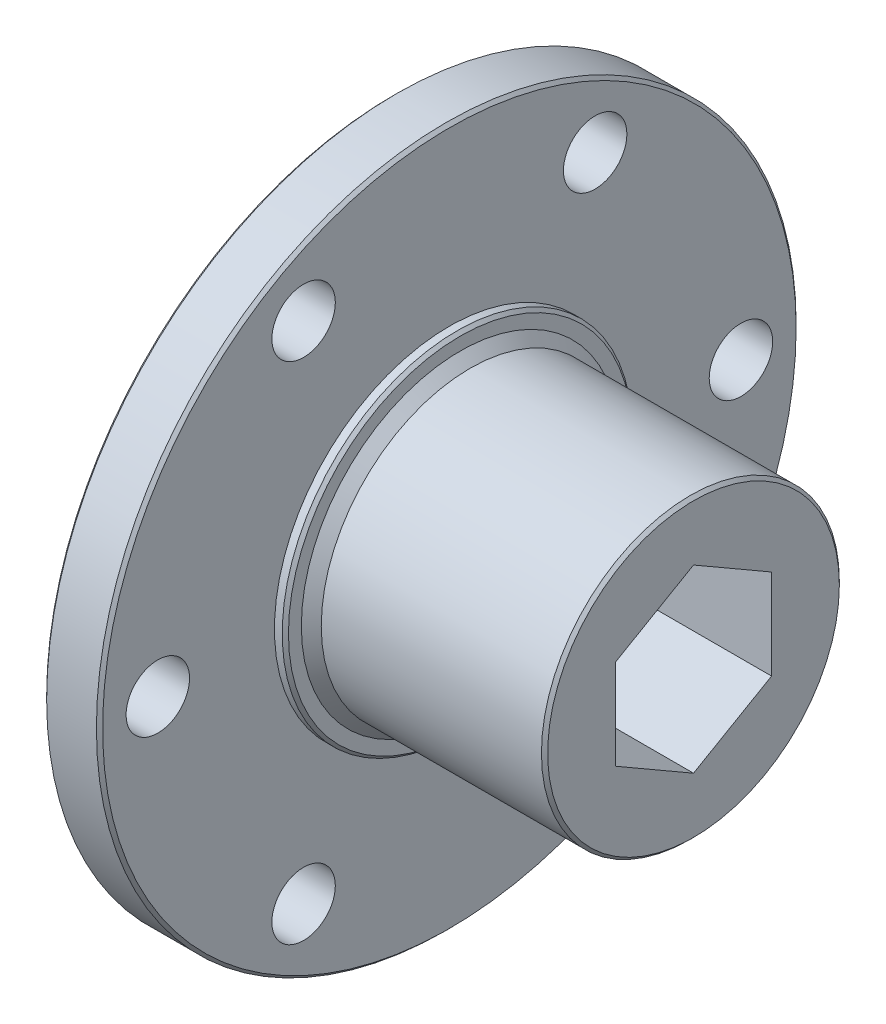
SolidWorks part; units mm, degrees
ref_plane "Front Plane" through (0, 0, 0) normal (0, 0, 1) x (1, 0, 0)
ref_plane "Top Plane" through (0, 0, 0) normal (0, 1, 0) x (1, 0, 0)
ref_plane "Right Plane" through (0, 0, 0) normal (1, 0, 0) x (0, 0, -1)
ref_plane "Plane4" through (0, 0, 0) normal (0, 0, -1) x (-1, 0, 0)
sketch "Sketch1" plane through (0, 0, 0) normal (0, 0, -1) x (-1, 0, 0)
  line L0 (13.9241, 28.575) -> (13.9241, 0)
  line L1 (13.9241, 0) -> (18.4961, 0)
  line L2 (18.4961, 0) -> (18.4961, 28.575)
  line L3 (18.4961, 28.575) -> (13.9241, 28.575)
  line L4 (13.9241, 0) -> (18.4961, 0) construction
revolve "Revolve1" add sketch "Sketch1" angle 360 about L4
sketch "Sketch2" plane through (-13.9241, 0, 0) normal (1, 0, 0) x (0, 0, -1)
  circle A0 centre (0, 0) radius 14.2875
extrude "Boss-Extrude1" add sketch "Sketch2" along normal blind 0.889
sketch "Sketch3" plane through (-13.0351, 0, 0) normal (1, 0, 0) x (0, 0, -1)
  circle A0 centre (0, 0) radius 12.9794
extrude "Boss-Extrude2" add sketch "Sketch3" along normal blind 0.8128 draft 45
sketch "Sketch4" plane through (-12.2223, 0, 0) normal (1, 0, 0) x (0, 0, -1)
  circle A0 centre (0, 0) radius 12.1666
extrude "Boss-Extrude3" add sketch "Sketch4" along normal blind 18.2372
sketch "Sketch5" plane through (-18.4961, 0, 0) normal (-1, 0, 0) x (0, 0, 1)
  circle A0 centre (0, 0) radius 14.2875
extrude "Boss-Extrude4" add sketch "Sketch5" along normal blind 0.889
sketch "Sketch6" plane through (-19.3851, 0, 0) normal (-1, 0, 0) x (0, 0, 1)
  line L0 (0, 7.3617) -> (-6.3754, 3.6808)
  line L1 (-6.3754, 3.6808) -> (-6.3754, -3.6809)
  line L2 (-6.3754, -3.6809) -> (0, -7.3617)
  line L3 (0, -7.3617) -> (6.3754, -3.6809)
  line L4 (6.3754, -3.6809) -> (6.3754, 3.6808)
  line L5 (6.3754, 3.6808) -> (0, 7.3617)
extrude "Cut-Extrude1" cut sketch "Sketch6" against normal through all
hole_wizard "#6 (0.204) Diameter Hole1" positions "Sketch8" profile "Sketch7" hole size "#6" standard "ANSI Inch"
sketch "Sketch8" plane through (-18.4961, 0, 0) normal (-1, 0, 0) x (0, 0, 1)
  point P0 (11.9063, 20.6222)
  point P1 (-23.8125, 0)
  point P2 (11.9062, -20.6222)
  point P3 (-11.9063, -20.6222)
  point P4 (-11.9062, 20.6222)
  point P5 (23.8125, 0)
sketch "Sketch7" plane through (-18.4961, 20.6222, 11.9063) normal (0, 1, 0) x (0, 0, 1)
  line L0 (0, 0) -> (0, 24.511)
  line L1 (0, 24.511) -> (2.5908, 24.511)
  line L2 (2.5908, 24.511) -> (2.5908, 0)
  line L5 (2.5908, 0) -> (0, 0)
  line L11 (0, -6.35) -> (0, 107.95) construction
  dimension "Thru Hole Dia." = 5.1816
  dimension "Thru Hole Depth" = 24.511
chamfer "Chamfer1" distance 0.254 angle 45 5 edges at (-19.3851, 0, 14.2875) (6.0149, 0, -12.1666) (-18.4961, 0, 28.575) (-13.0351, 0, -14.2875) (-13.9241, 0, 28.575)
